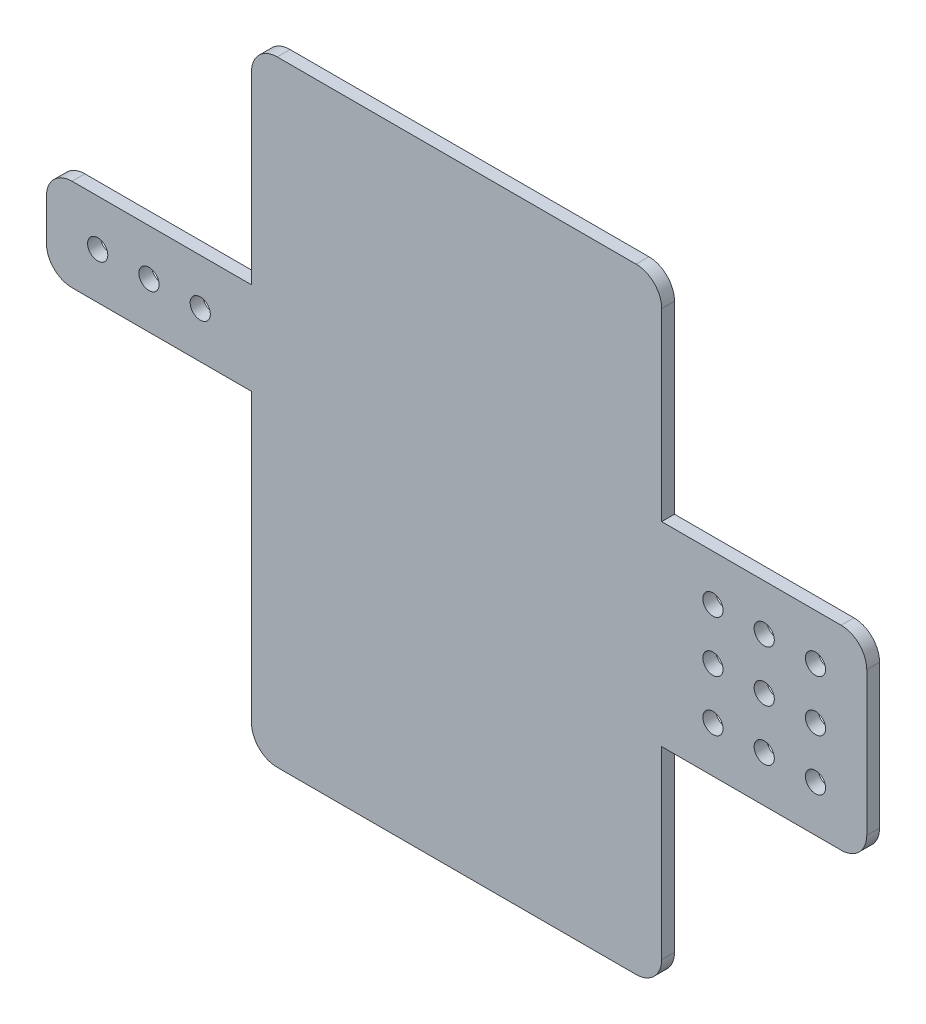
SolidWorks part; units mm, degrees
ref_plane "Front Plane" through (0, 0, 0) normal (0, 0, 1) x (1, 0, 0)
ref_plane "Top Plane" through (0, 0, 0) normal (0, 1, 0) x (1, 0, 0)
ref_plane "Right Plane" through (0, 0, 0) normal (1, 0, 0) x (0, 0, -1)
sketch "Sketch1" plane through (0, 0, 0) normal (0, 0, 1) x (1, 0, 0)
  line L1 (-125.1762, 25.1031) -> (-36.2762, 25.1031)
  line L2 (-131.5262, 18.7531) -> (-131.5262, -120.9469)
  line L3 (-125.1762, -127.2969) -> (-36.2762, -127.2969)
  line L4 (-29.9262, 18.7531) -> (-29.9262, -120.9469)
  line L5 (-29.9262, -26.9669) -> (14.5238, -26.9669)
  line L6 (-29.9262, -26.9669) -> (-29.9262, -75.2269)
  line L7 (-29.9262, -75.2269) -> (14.5238, -75.2269)
  line L8 (20.8738, -33.3169) -> (20.8738, -68.8769)
  line L9 (-131.5262, -26.9669) -> (-175.9762, -26.9669)
  line L10 (-131.5262, -26.9669) -> (-131.5262, -49.8269)
  line L11 (-131.5262, -49.8269) -> (-175.9762, -49.8269)
  line L12 (-182.3262, -33.3169) -> (-182.3262, -43.4769)
  arc A0 (-175.9762, -26.9669) -> (-182.3262, -33.3169) centre (-175.9762, -33.3169) ccw
  arc A1 (-175.9762, -49.8269) -> (-182.3262, -43.4769) centre (-175.9762, -43.4769) cw
  arc A2 (-131.5262, -120.9469) -> (-125.1762, -127.2969) centre (-125.1762, -120.9469) ccw
  arc A3 (-36.2762, -127.2969) -> (-29.9262, -120.9469) centre (-36.2762, -120.9469) ccw
  arc A4 (14.5238, -75.2269) -> (20.8738, -68.8769) centre (14.5238, -68.8769) ccw
  arc A5 (14.5238, -26.9669) -> (20.8738, -33.3169) centre (14.5238, -33.3169) cw
  arc A6 (-36.2762, 25.1031) -> (-29.9262, 18.7531) centre (-36.2762, 18.7531) cw
  arc A7 (-125.1762, 25.1031) -> (-131.5262, 18.7531) centre (-125.1762, 18.7531) ccw
  point P14 (-182.3262, -26.9669)
  point P17 (-182.3262, -49.8269)
  point P20 (-131.5262, -127.2969)
  point P23 (-29.9262, -127.2969)
  point P26 (20.8738, -75.2269)
  point P29 (20.8738, -26.9669)
  point P32 (-29.9262, 25.1031)
  dimension "D7" = 6.35
  dimension "D8" = 44.45
  dimension "D1" = 101.6
  dimension "D2" = 152.4
  dimension "D3" = 48.26
  dimension "D4" = 52.07
  dimension "D5" = 22.86
  dimension "D6" = 52.07
  dimension "D9" = 44.45
extrude "Boss-Extrude1" add sketch "Sketch1" along normal blind 3.175 contours L1 A7 L2 A2 L3 A3 L4 A6 | A1 L11 L2 L9 A0 L12 | A5 L5 L4 L7 A4 L8
sketch "Sketch2" plane through (0, 0, 3.175) normal (0, 0, 1) x (1, 0, 0)
  line L0 (-131.5262, -49.8269) -> (-175.9762, -49.8269) construction
  line L1 (-182.3262, -33.3169) -> (-182.3262, -43.4769) construction
  line L2 (20.8738, -33.3169) -> (20.8738, -68.8769) construction
  line L3 (-29.9262, -75.2269) -> (14.5238, -75.2269) construction
  circle A0 centre (-169.6262, -38.3969) radius 2.5
  circle A1 centre (8.1738, -63.7969) radius 2.5
  circle A2 centre (-156.9262, -38.3969) radius 2.5
  circle A3 centre (-144.2262, -38.3969) radius 2.5
  circle A4 centre (-4.5262, -63.7969) radius 2.5
  circle A5 centre (-17.2262, -63.7969) radius 2.5
  circle A6 centre (-4.5262, -51.0969) radius 2.5
  circle A7 centre (-17.2262, -51.0969) radius 2.5
  circle A8 centre (-4.5262, -38.3969) radius 2.5
  circle A9 centre (-17.2262, -38.3969) radius 2.5
  circle A10 centre (8.1738, -51.0969) radius 2.5
  circle A11 centre (8.1738, -38.3969) radius 2.5
  dimension "D1" = 5
  dimension "D2" = 11.43
  dimension "D6" = 5
  dimension "D3" = 12.7
  dimension "D4" = 12.7
  dimension "D5" = 11.43
  dimension "D7" = 3
  dimension "D8" = 3
  dimension "D9" = 3
extrude "Cut-Extrude1" cut sketch "Sketch2" against normal through all
